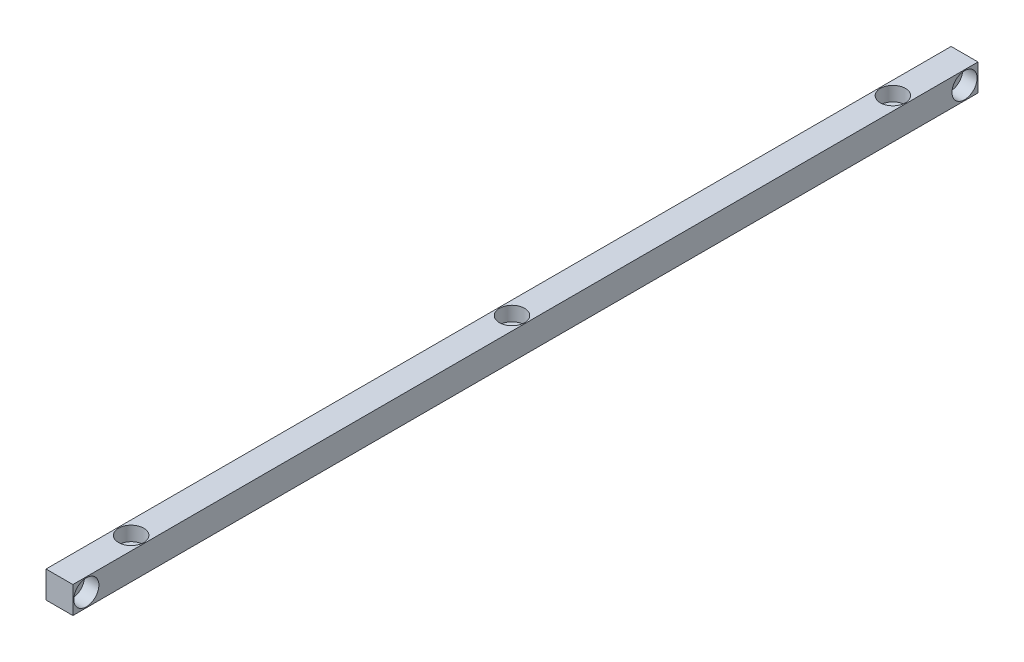
SolidWorks part; units mm, degrees
ref_plane "Front Plane" through (0, 0, 0) normal (0, 0, 1) x (1, 0, 0)
ref_plane "Top Plane" through (0, 0, 0) normal (0, 1, 0) x (1, 0, 0)
ref_plane "Right Plane" through (0, 0, 0) normal (1, 0, 0) x (0, 0, -1)
sketch "Çizim1" plane through (0, 0, 0) normal (0, 0, 1) x (1, 0, 0)
  line L1 (-7.5, 7.5) -> (7.5, 7.5)
  line L2 (-7.5, 7.5) -> (-7.5, -7.5)
  line L3 (-7.5, -7.5) -> (7.5, -7.5)
  line L4 (7.5, 7.5) -> (7.5, -7.5)
  line L5 (-7.5, 7.5) -> (7.5, -7.5) construction
  line L6 (-7.5, -7.5) -> (7.5, 7.5) construction
  point P0 (0, 0)
  dimension "D1" = 15
extrude "Yükseklik-Ekstrüzyon1" add sketch "Çizim1" along normal mid plane 505
hole_wizard "Delik2" positions "Çizim5" profile "Çizim6" legacy
sketch "Çizim5" plane through (7.5, 0, 0) normal (1, 0, 0) x (0, 0, -1)
  line L0 (252.5, -7.5) -> (252.5, 7.5) construction
  line L1 (-252.5, 7.5) -> (252.5, 7.5) construction
  point P0 (245, 0)
  dimension "D1" = 7.5
  dimension "D2" = 7.5
sketch "Çizim6" plane through (7.5, 0, -245) normal (0, 1, 0) x (0, 0, -1)
  line L0 (0, 0) -> (0, 15)
  line L1 (0, 15) -> (4.25, 15)
  line L2 (4.25, 15) -> (4.25, 8)
  line L3 (4.25, 8) -> (7, 8)
  line L4 (7, 8) -> (7, 0)
  line L5 (7, 0) -> (0, 0)
  line L6 (0, 110) -> (0, -10) construction
  dimension "Diameter" = 8.5
  dimension "Depth" = 15
  dimension "C-Bore Diameter" = 14
  dimension "C-Bore Depth" = 8
mirror "Aynalama1" about plane through (0, 0, 0) normal (0, 0, 1) of "Delik2"
hole_wizard "Delik3" positions "Çizim7" profile "Çizim8" legacy
sketch "Çizim7" plane through (0, 7.5, 0) normal (0, 1, 0) x (1, 0, 0)
  line L0 (7.5, -252.5) -> (-7.5, -252.5) construction
  point P3 (0, -212.5)
  dimension "D1" = 40
sketch "Çizim8" plane through (0, 7.5, 212.5) normal (1, 0, 0) x (0, 0, 1)
  line L0 (0, 0) -> (0, 15)
  line L1 (0, 15) -> (4.25, 15)
  line L2 (4.25, 15) -> (4.25, 8)
  line L3 (4.25, 8) -> (7, 8)
  line L4 (7, 8) -> (7, 0)
  line L5 (7, 0) -> (0, 0)
  line L6 (0, 110) -> (0, -10) construction
  dimension "Diameter" = 8.5
  dimension "Depth" = 15
  dimension "C-Bore Diameter" = 14
  dimension "C-Bore Depth" = 8
pattern_linear "LÇoğaltma1" count 3 spacing 212.5 along (0, 0, -1) of "Delik3"
